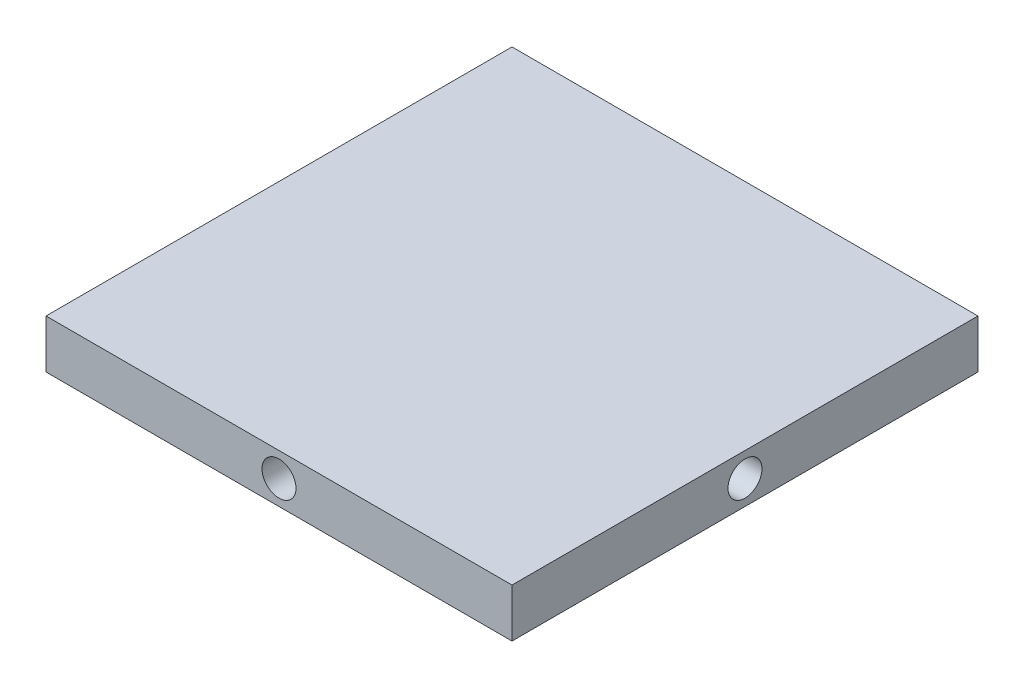
SolidWorks part; units mm, degrees
ref_plane "前视基准面" through (0, 0, 0) normal (0, 0, 1) x (1, 0, 0)
ref_plane "上视基准面" through (0, 0, 0) normal (0, 1, 0) x (1, 0, 0)
ref_plane "右视基准面" through (0, 0, 0) normal (1, 0, 0) x (0, 0, -1)
sketch "草图1" plane through (0, 0, 0) normal (0, 1, 0) x (1, 0, 0)
  line L1 (-48, -48) -> (48, -48)
  line L2 (-48, -48) -> (-48, 48)
  line L3 (-48, 48) -> (48, 48)
  line L4 (48, -48) -> (48, 48)
  line L5 (-48, -48) -> (48, 48) construction
  line L6 (-48, 48) -> (48, -48) construction
  point P0 (0, 0)
extrude "凸台-拉伸1" add sketch "草图1" along normal blind 10
sketch "草图2" plane through (0, 0, 48) normal (0, 0, 1) x (1, 0, 0)
  line L0 (-48, 10) -> (48, 0)
  line L1 (-48, 0) -> (48, 0) construction
  line L2 (48, 10) -> (48, 0) construction
  line L3 (48, 0) -> (48, 10)
  line L4 (48, 10) -> (-48, 0)
  circle A0 centre (0, 5) radius 3.5
extrude "切除-拉伸1" cut sketch "草图2" against normal blind 10 contours A0
sketch "草图3" plane through (48, 0, 0) normal (1, 0, 0) x (0, 0, -1)
  line L0 (-48, 10) -> (48, 0)
  line L1 (48, 0) -> (48, 10)
  line L2 (48, 10) -> (-48, 0)
  circle A0 centre (0, 5) radius 3.5
extrude "切除-拉伸2" cut sketch "草图3" against normal blind 10 contours A0
sketch "草图4" plane through (0, 0, -48) normal (0, 0, -1) x (-1, 0, 0)
  line L0 (-48, 10) -> (48, 0)
  line L1 (48, 0) -> (48, 10)
  line L2 (48, 10) -> (-48, 0)
  circle A0 centre (0, 5) radius 3.5
extrude "切除-拉伸3" cut sketch "草图4" against normal blind 10 contours L2 A0 L0 | L2 A0 L0 | L0 A0 L2 | L0 A0 L2
sketch "草图5" plane through (-48, 0, 0) normal (-1, 0, 0) x (0, 0, 1)
  line L0 (-48, 10) -> (48, 0)
  line L1 (48, 0) -> (48, 10)
  line L2 (48, 10) -> (-48, 0)
  circle A0 centre (0, 5) radius 3.5
extrude "切除-拉伸4" cut sketch "草图5" against normal blind 10 contours A0
